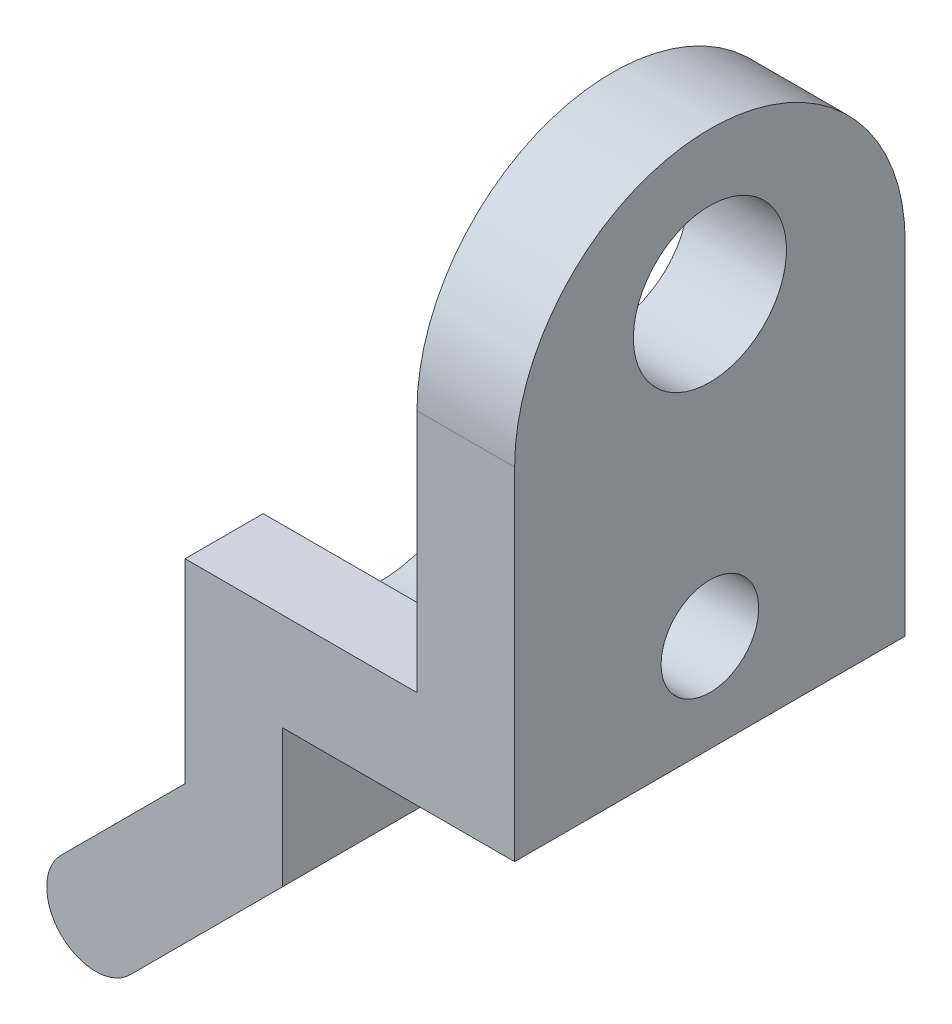
SolidWorks part; units mm, degrees
ref_plane "Front Plane" through (0, 0, 0) normal (0, 0, 1) x (1, 0, 0)
ref_plane "Top Plane" through (0, 0, 0) normal (0, 1, 0) x (1, 0, 0)
ref_plane "Right Plane" through (0, 0, 0) normal (1, 0, 0) x (0, 0, -1)
sketch "Sketch1" plane through (0, 0, 0) normal (0, 0, 1) x (1, 0, 0)
  line L0 (-9.525, -3.175) -> (-6.35, -6.35)
  line L1 (-9.525, 0) -> (9.525, 0)
  line L2 (-9.525, 0) -> (-9.525, -6.35) construction
  line L3 (-9.525, -6.35) -> (9.525, -6.35) construction
  line L4 (9.525, 0) -> (9.525, -6.35) construction
  line L5 (0, 0) -> (0, -6.35) construction
  line L6 (9.525, -3.175) -> (6.35, -6.35)
  line L7 (-9.525, -3.175) -> (-9.525, 0)
  line L8 (-6.35, -6.35) -> (6.35, -6.35)
  line L9 (9.525, 0) -> (9.525, -3.175)
  dimension "D1" = 19.05
  dimension "D2" = 6.35
  dimension "D3" = 135
sketch "Sketch2" plane through (0, 0, 0) normal (0, 0, 1) x (1, 0, 0)
  line L0 (-9.3407, -3.3593) -> (-6.5343, -6.1657)
  line L1 (-9.3407, -3.3593) -> (-16.0759, -10.0945)
  line L2 (-6.5343, -6.1657) -> (-13.2695, -12.9009)
  line L3 (-16.0759, -10.0945) -> (-13.2695, -12.9009)
  line L4 (-9.525, -3.175) -> (-6.35, -6.35) construction
  line L5 (-11.1125, -2.8861) -> (-11.1125, 1.5875)
  line L6 (-11.1125, -2.8861) -> (-16.0759, -7.8495)
  line L7 (-9.525, -3.175) -> (-9.525, 0) construction
  line L8 (-9.9019, -9.5333) -> (-13.8308, -5.6044) construction
  line L9 (-8.7794, -8.4107) -> (-12.7083, -4.4819)
  line L10 (-11.0245, -10.6558) -> (-14.9533, -6.7269)
  line L11 (-12.9889, -8.6914) -> (-10.7438, -6.4463) construction
  line L12 (-11.1125, 1.5875) -> (0, 1.5875)
  line L13 (-9.525, 0) -> (9.525, 0) construction
  line L14 (-14.2875, -1.571) -> (-18.3209, -5.6044)
  line L15 (-14.2875, -1.571) -> (-14.2875, 4.7625)
  line L16 (-14.2875, 4.7625) -> (0, 4.7625)
  line L17 (0, 1.5875) -> (0, 4.7625)
  arc A0 (-18.3209, -5.6044) -> (-16.0759, -7.8495) centre (-17.1984, -6.7269) ccw
  point P6 (-7.9375, -4.7625)
  point P7 (-7.9375, -4.7625)
  point P21 (-11.8664, -7.5688)
  dimension "D1" = 3.9688
  dimension "D2" = 9.525
  dimension "D3" = 1.5875
  dimension "D4" = 1.5875
  dimension "D5" = 3.175
  dimension "D6" = 1.5875
  dimension "D7" = 3.175
extrude "Boss-Extrude1" add sketch "Sketch2" along normal mid plane 12.7 contours L14 A0 L6 L5 L12 L17 L16 L15
sketch "Sketch3" plane through (-4.1132, 4.1132, 0) normal (0.7071, -0.7071, 0) x (0, 0, -1)
  circle A0 centre (0, -13.7428) radius 1.5875
  dimension "D1" = 3.175
extrude "Cut-Extrude1" cut sketch "Sketch3" against normal through all both and the other way through all
sketch "Sketch4" plane through (0, 0, 0) normal (0, 0, 1) x (1, 0, 0)
  line L0 (0, 0) -> (0, -6.35) construction
  line L1 (-1.9844, 9.525) -> (1.9844, 9.525)
  line L2 (-1.9844, 9.525) -> (-1.9844, 0)
  line L3 (-1.9844, 0) -> (1.9844, 0)
  line L4 (1.9844, 9.525) -> (1.9844, 0)
  line L5 (-9.525, 0) -> (9.525, 0) construction
  line L6 (-1.9844, 4.7625) -> (1.9844, 4.7625) construction
  line L7 (-11.1125, 1.5875) -> (0, 1.5875) construction
  line L8 (-3.5719, 1.5875) -> (-6.7469, 1.5875)
  line L9 (-3.5719, 1.5875) -> (-3.5719, 9.525)
  line L10 (-3.5719, 9.525) -> (-6.7469, 9.525)
  line L11 (-6.7469, 1.5875) -> (-6.7469, 9.525)
  point P4 (0, 0)
  dimension "D1" = 3.9688
  dimension "D2" = 9.525
  dimension "D3" = 1.5875
  dimension "D4" = 3.175
extrude "Boss-Extrude3" add sketch "Sketch4" along normal mid plane 12.7 contours L11 L8 L9 L10
sketch "Sketch5" plane through (-14.2875, 0, 0) normal (-1, 0, 0) x (0, 0, 1)
  line L0 (6.35, 4.7625) -> (-6.35, 4.7625) construction
  circle A0 centre (0, 4.7625) radius 3.81
  dimension "D1" = 7.62
extrude "Cut-Extrude2" cut sketch "Sketch5" against normal up to surface (7.5406 mm away) up to face at (-6.7469, 7.1438, 0)
sketch "Sketch6" plane through (-14.2875, 0, 0) normal (-1, 0, 0) x (0, 0, 1)
  circle A0 centre (0, 4.7625) radius 1.5875
  dimension "D1" = 3.175
extrude "Cut-Extrude3" cut sketch "Sketch6" against normal through all
sketch "Sketch7" plane through (0, 0, 6.35) normal (0, 0, 1) x (1, 0, 0)
  line L1 (-3.5719, 4.7625) -> (0, 4.7625)
  line L2 (-3.5719, 4.7625) -> (-3.5719, 1.5875)
  line L3 (-3.5719, 1.5875) -> (0, 1.5875)
  line L4 (0, 4.7625) -> (0, 1.5875)
extrude "Cut-Extrude4" cut sketch "Sketch7" against normal through all
sketch "Sketch8" plane through (-3.5719, 0, 0) normal (1, 0, 0) x (0, 0, -1)
  line L0 (6.35, 1.5875) -> (6.35, 9.525) construction
  line L1 (-6.35, 1.5875) -> (-6.35, 9.525) construction
  line L2 (-6.35, 9.525) -> (6.35, 9.525) construction
  line L3 (-6.35, 9.525) -> (-6.35, 12.7)
  line L4 (6.35, 9.525) -> (6.35, 12.7)
  circle A0 centre (0, 12.7) radius 6.35
  line M4 (6.35, 9.525) -> (-6.35, 9.525)
  dimension "D1" = 3.175
extrude "Boss-Extrude4" add sketch "Sketch8" against normal up to surface (3.175 mm away) contours A0 M4 | A0 L3 M4 | A0 L4 M4 up to face at (-6.7469, 4.7625, 1.5875)
sketch "Sketch9" plane through (-6.7469, 0, 0) normal (-1, 0, 0) x (0, 0, 1)
  line L0 (6.35, 12.7) -> (-5.4993, 15.875)
  line L1 (-6.35, 12.7) -> (5.4993, 15.875)
  arc A0 (6.35, 12.7) -> (-6.35, 12.7) centre (0, 12.7) ccw construction
  circle A1 centre (0, 14.4015) radius 2.4892
  point P9 (0.629, 15.0697)
  dimension "D2" = 4.9784
  dimension "D1" = 30
extrude "Cut-Extrude5" cut sketch "Sketch9" against normal through all both and the other way through all contours L1 A1 L0 | L0 A1 L1 | L0 A1 L1 | L1 A1 L0
